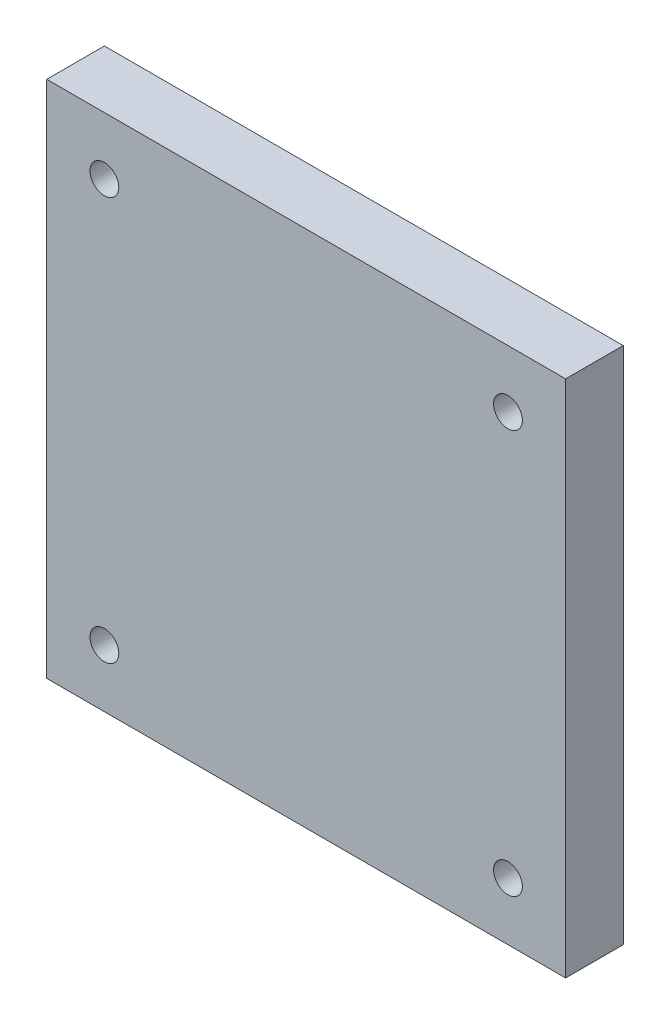
SolidWorks part; units mm, degrees
ref_plane "Plan de face" through (0, 0, 0) normal (0, 0, 1) x (1, 0, 0)
ref_plane "Plan de dessus" through (0, 0, 0) normal (0, 1, 0) x (1, 0, 0)
ref_plane "Plan de droite" through (0, 0, 0) normal (1, 0, 0) x (0, 0, -1)
sketch "Esquisse1" plane through (0, 0, 0) normal (0, 0, 1) x (1, 0, 0)
  line L1 (0, 45) -> (45, 45)
  line L2 (0, 45) -> (0, 0)
  line L3 (0, 0) -> (45, 0)
  line L4 (45, 45) -> (45, 0)
  dimension "D1" = 45
  dimension "D2" = 45
extrude "Boss.-Extru.1" add sketch "Esquisse1" along normal blind 5
hole_wizard "Trou pour taraudage pour trou taraudé M3x0.51" positions "Esquisse3" profile "Esquisse2" hole size "M3x0.5" standard "Ansi Métrique"
sketch "Esquisse3" plane through (0, 0, 5) normal (0, 0, 1) x (1, 0, 0)
  line L5 (45, 45) -> (0, 45) construction
  line L6 (0, 45) -> (0, 0) construction
  line L7 (45, 0) -> (45, 45) construction
  line L10 (0, 0) -> (45, 0) construction
  point P0 (5, 40)
  point P28 (40, 5)
  point P30 (40, 40)
  point P57 (5, 5)
  dimension "D1" = 5
  dimension "D2" = 5
  dimension "D3" = 5
  dimension "D4" = 5
  dimension "D5" = 5
  dimension "D6" = 5
  dimension "D7" = 5
  dimension "D8" = 5
sketch "Esquisse2" plane through (5, 40, 5) normal (1, 0, 0) x (0, -1, 0)
  line L0 (0, 0) -> (0, 10.7511)
  line L1 (0, 10.7511) -> (1.25, 10)
  line L2 (1.25, 10) -> (1.25, 0)
  line L5 (1.25, 0) -> (0, 0)
  line L10 (0, 10.7511) -> (-1.25, 10) construction
  line L11 (0, -6.35) -> (0, 107.95) construction
  dimension "Diamètre du perçage" = 2.5
  dimension "Profondeur du perçage" = 10
  dimension "Angle de pointe" = 118
